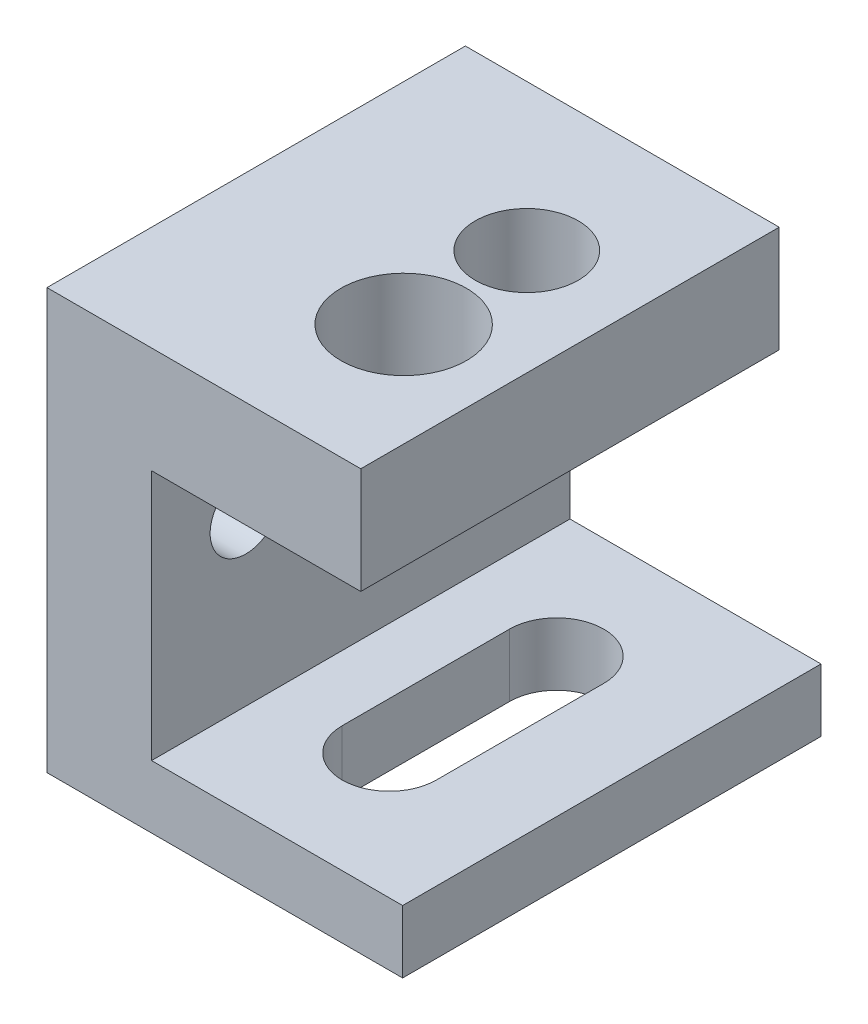
SolidWorks part; units mm, degrees
ref_plane "Front Plane" through (0, 0, 0) normal (0, 0, 1) x (1, 0, 0)
ref_plane "Top Plane" through (0, 0, 0) normal (0, 1, 0) x (1, 0, 0)
ref_plane "Right Plane" through (0, 0, 0) normal (1, 0, 0) x (0, 0, -1)
sketch "Sketch1" plane through (0, 0, 0) normal (0, 1, 0) x (1, 0, 0)
  line L1 (7.5, -10) -> (-7.5, -10)
  line L2 (7.5, -10) -> (7.5, 10)
  line L3 (7.5, 10) -> (-7.5, 10)
  line L4 (-7.5, -10) -> (-7.5, 10)
  line L5 (7.5, -10) -> (-7.5, 10) construction
  line L6 (7.5, 10) -> (-7.5, -10) construction
  point P0 (0, 0)
  dimension "D1" = 20
  dimension "D2" = 15
extrude "Boss-Extrude1" add sketch "Sketch1" along normal blind 5.08
sketch "Sketch2" plane through (0, 0, 0) normal (0, -1, 0) x (-1, 0, 0)
  line L0 (7.5, -10) -> (-7.5, -10) construction
  line L1 (7.5, 10) -> (2.5, 10)
  line L2 (7.5, 10) -> (7.5, -10)
  line L3 (7.5, -10) -> (2.5, -10)
  line L4 (2.5, 10) -> (2.5, -10)
  dimension "D1" = 5
extrude "Boss-Extrude2" add sketch "Sketch2" along normal blind 15
sketch "Sketch3" plane through (0, 5.08, 0) normal (0, 1, 0) x (1, 0, 0)
  line L0 (7.5, 10) -> (-7.5, 10) construction
  circle A0 centre (2.4352, 3) radius 2.4638
  dimension "D1" = 7
sketch "Sketch4" plane through (0, 5.08, 0) normal (0, 1, 0) x (1, 0, 0)
  circle A0 centre (2.5512, -3) radius 3
  dimension "D1" = 6
hole_wizard "M3 Clearance Hole1" positions "Sketch6" profile "Sketch5" hole size "M3" standard "ANSI Metric" end condition through all
sketch "Sketch6" plane through (-2.5, 0, 0) normal (1, 0, 0) x (0, 0, -1)
  line L0 (10, -15) -> (10, 0) construction
  line L1 (-10, -15) -> (-10, 0) construction
  line L2 (10, 0) -> (-10, 0) construction
  point P0 (5.5, -4)
  point P2 (-5.5, -4)
  dimension "D1" = 4.5
  dimension "D2" = 4.5
  dimension "D3" = 4
  dimension "D4" = 4
sketch "Sketch5" plane through (-2.5, -4, -5.5) normal (0, 1, 0) x (0, 0, -1)
  line L0 (0, 0) -> (0, 5)
  line L1 (0, 5) -> (1.7, 5)
  line L2 (1.7, 5) -> (1.7, 0)
  line L5 (1.7, 0) -> (0, 0)
  line L11 (0, -6.35) -> (0, 107.95) construction
  dimension "Thru Hole Dia." = 3.4
  dimension "Thru Hole Depth" = 5
sketch "Sketch7" plane through (-2.5, 0, 0) normal (1, 0, 0) x (0, 0, -1)
  line L0 (-10, -15) -> (-10, 0) construction
  line L1 (10, -15) -> (-10, -15)
  line L2 (10, -15) -> (10, -12)
  line L3 (10, -12) -> (-10, -12)
  line L4 (-10, -15) -> (-10, -12)
  dimension "D1" = 3
extrude "Boss-Extrude3" add sketch "Sketch7" along normal blind 12
extrude "Cut-Extrude1" cut sketch "Sketch3" against normal blind 12 contours A0
extrude "Cut-Extrude2" cut sketch "Sketch4" against normal blind 12 contours A0
sketch "Sketch8" plane through (0, -15, 0) normal (0, -1, 0) x (-1, 0, 0)
  line L0 (-2.8615, 4) -> (-2.8615, -4) construction
  line L1 (-0.6115, 4) -> (-0.6115, -4)
  line L2 (-5.1115, 4) -> (-5.1115, -4)
  line L3 (-9.5, -10) -> (7.5, -10) construction
  line L4 (7.5, 10) -> (-9.5, 10) construction
  arc A0 (-0.6115, 4) -> (-5.1115, 4) centre (-2.8615, 4) ccw
  arc A1 (-5.1115, -4) -> (-0.6115, -4) centre (-2.8615, -4) ccw
  point P2 (-2.8615, 0)
  dimension "D1" = 6
  dimension "D2" = 6
  dimension "D3" = 4.5
extrude "Cut-Extrude3" cut sketch "Sketch8" against normal blind 12
